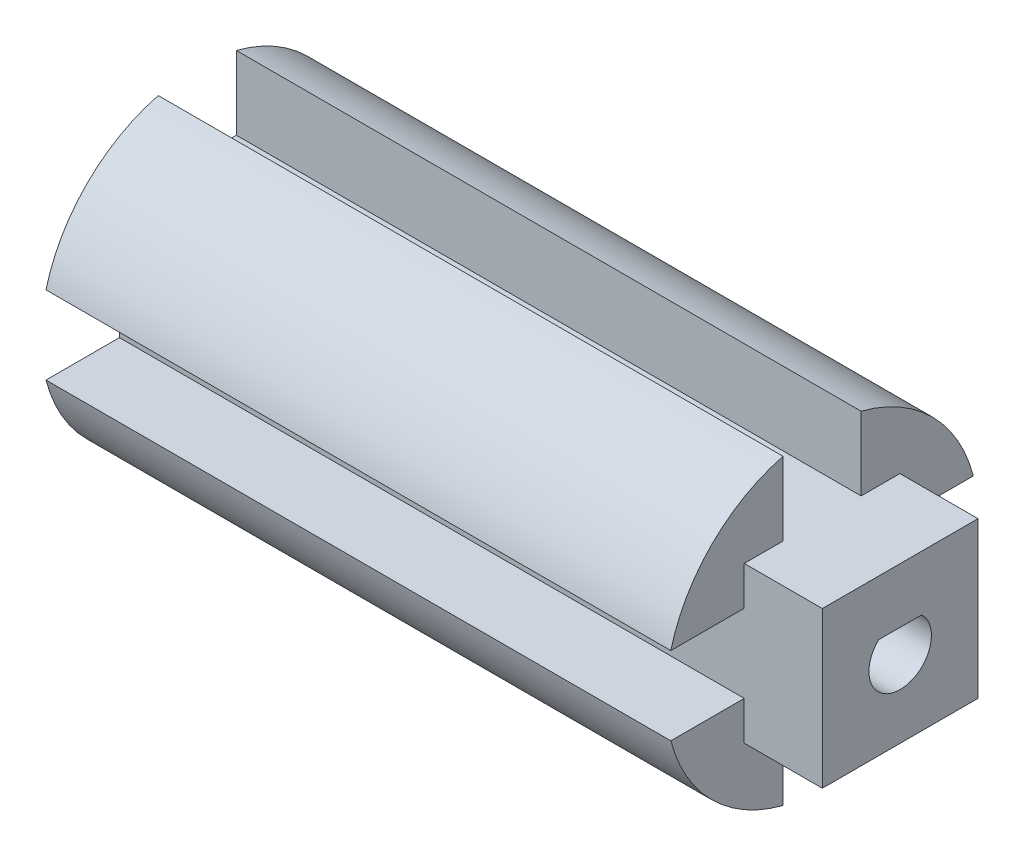
SolidWorks part; units mm, degrees
ref_plane "Front Plane" through (0, 0, 0) normal (0, 0, 1) x (1, 0, 0)
ref_plane "Top Plane" through (0, 0, 0) normal (0, 1, 0) x (1, 0, 0)
ref_plane "Right Plane" through (0, 0, 0) normal (1, 0, 0) x (0, 0, -1)
sketch "Sketch1" plane through (0, 0, 0) normal (1, 0, 0) x (0, 0, -1)
  line L1 (-5, -19.3649) -> (-5, -9.9649)
  line L2 (5, -19.3649) -> (5, -9.9649)
  line L4 (-19.3649, 5) -> (-9.9649, 5)
  line L5 (-19.3649, -5) -> (-9.9649, -5)
  line L7 (-5, 9.9649) -> (5, 9.9649)
  line L8 (9.9649, 5) -> (9.9649, -5)
  line L9 (-5, -9.9649) -> (5, -9.9649)
  line L10 (-9.9649, 5) -> (-9.9649, -5)
  line L11 (-5, 9.9649) -> (-5, 19.3649)
  line L13 (5, 9.9649) -> (5, 19.3649)
  line L16 (9.9649, -5) -> (19.3649, -5)
  line L18 (9.9649, 5) -> (19.3649, 5)
  circle A0 centre (0, 0) radius 20
  dimension "D1" = 40
  dimension "D2" = 10
  dimension "D3" = 10
  dimension "D4" = 10
  dimension "D5" = 9.4
  dimension "D6" = 9.4
  dimension "D7" = 9.4
  dimension "D8" = 9.4
  dimension "D9" = 9.4
extrude "Extruded Connector" add sketch "Sketch1" along normal blind 90 contours L18 A0 L13 L7 L11 L4 L10 L5 L1 L9 L2 L16 L8
sketch "Sketch10" plane through (90, 0, 0) normal (1, 0, 0) x (0, 0, -1)
  line L0 (-2.755, 2.9) -> (2.755, 2.9)
  arc A0 (-2.755, 2.9) -> (2.755, 2.9) centre (0, 0) ccw
  dimension "D1" = 8
  dimension "D2" = 2.9
extrude "Key Cut" cut sketch "Sketch10" against normal blind 18
sketch "Sketch11" plane through (90, 0, 0) normal (1, 0, 0) x (0, 0, -1)
  line L0 (9.9649, 5) -> (9.9649, -5) construction
  line L3 (-9.9649, 5) -> (-19.3649, 5)
  line L4 (-9.9649, 5) -> (-9.9649, -5)
  line L5 (-9.9649, -5) -> (-19.3649, -5)
  line L6 (-19.3649, 5) -> (-19.3649, -5)
  line L7 (-5, 9.9649) -> (5, 9.9649)
  line L8 (-5, 9.9649) -> (-5, 19.3649)
  line L9 (-5, 19.3649) -> (5, 19.3649)
  line L10 (5, 9.9649) -> (5, 19.3649)
  line L11 (9.9649, 5) -> (19.3649, 5)
  line L12 (9.9649, 5) -> (9.9649, -5)
  line L13 (9.9649, -5) -> (19.3649, -5)
  line L14 (19.3649, 5) -> (19.3649, -5)
  line L15 (5, -19.3649) -> (5, -9.9649) construction
  line L16 (-5, -9.9649) -> (5, -9.9649)
  line L17 (-5, -9.9649) -> (-5, -19.3649)
  line L18 (-5, -19.3649) -> (5, -19.3649)
  line L19 (5, -9.9649) -> (5, -19.3649)
  line L20 (-9.9649, -5) -> (-9.9649, -9.9649)
  line L21 (-9.9649, -9.9649) -> (-5, -9.9649)
  line L22 (5, -9.9649) -> (9.9649, -9.9649)
  line L23 (9.9649, -9.9649) -> (9.9649, -5)
  line L24 (9.9649, 5) -> (9.9649, 9.9649)
  line L25 (9.9649, 9.9649) -> (5, 9.9649)
  line L26 (-5, 9.9649) -> (-9.9649, 9.9649)
  line L27 (-9.9649, 9.9649) -> (-9.9649, 5)
  circle A0 centre (0, 0) radius 20
  line M3 (9.9649, 5) -> (19.3649, 5)
  arc M4 (19.3649, 5) -> (5, 19.3649) centre (0, 0) ccw
  line M5 (5, 19.3649) -> (5, 9.9649)
  line M7 (-5, 9.9649) -> (-5, 19.3649)
  arc M8 (-5, 19.3649) -> (-19.3649, 5) centre (0, 0) ccw
  line M9 (-19.3649, 5) -> (-9.9649, 5)
  line M11 (-9.9649, -5) -> (-19.3649, -5)
  arc M12 (-19.3649, -5) -> (-5, -19.3649) centre (0, 0) ccw
  line M13 (-5, -19.3649) -> (-5, -9.9649)
  line M15 (5, -9.9649) -> (5, -19.3649)
  arc M16 (5, -19.3649) -> (19.3649, -5) centre (0, 0) ccw
  line M17 (19.3649, -5) -> (9.9649, -5)
extrude "Cut-Extrude2" cut sketch "Sketch11" against normal blind 10 contours L27 L26 M7 M8 M9 | L25 L24 M3 M4 M5 | L23 L22 M15 M16 M17 | L21 L20 M11 M12 M13
